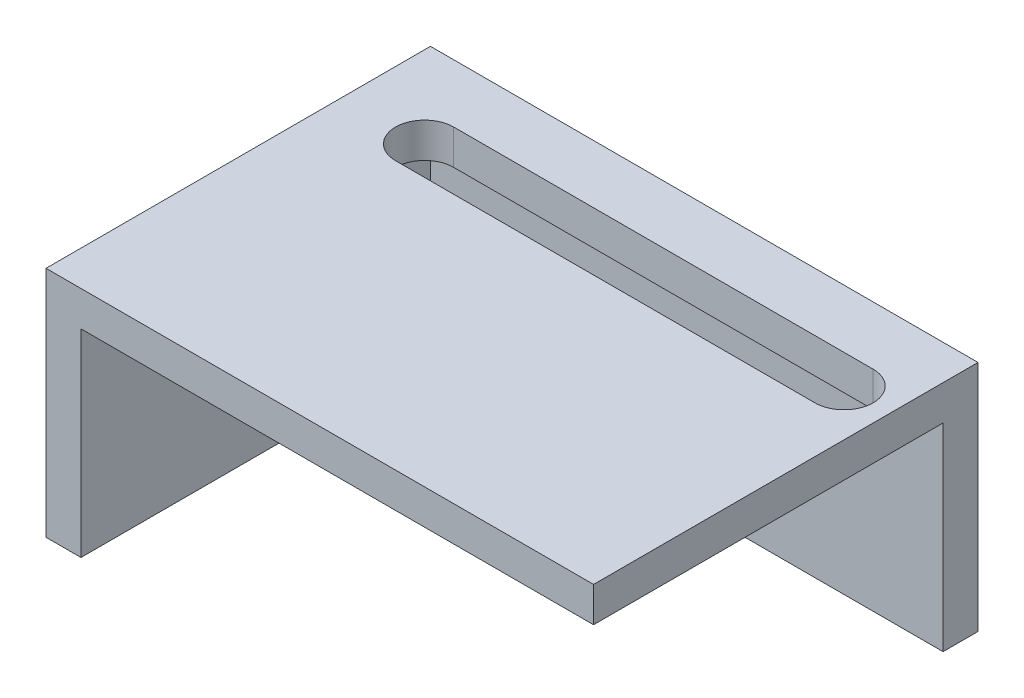
SolidWorks part; units mm, degrees
ref_plane "Front Plane" through (0, 0, 0) normal (0, 0, 1) x (1, 0, 0)
ref_plane "Top Plane" through (0, 0, 0) normal (0, 1, 0) x (1, 0, 0)
ref_plane "Right Plane" through (0, 0, 0) normal (1, 0, 0) x (0, 0, -1)
sketch "Sketch2" plane through (0, 0, 0) normal (0, 1, 0) x (1, 0, 0)
  line L1 (22, 15) -> (-22, 15)
  line L2 (22, 15) -> (22, -15)
  line L3 (22, -15) -> (-22, -15)
  line L4 (-22, 15) -> (-22, -15)
  line L5 (22, 15) -> (-22, -15) construction
  line L6 (22, -15) -> (-22, 15) construction
  point P0 (0, 0)
  dimension "D1" = 44
  dimension "D2" = 30
extrude "Boss-Extrude1" add sketch "Sketch2" along normal blind 3
sketch "Sketch3" plane through (0, 0, -15) normal (0, 0, -1) x (-1, 0, 0)
  line L1 (-22, 3) -> (22, 3)
  line L2 (-22, 3) -> (-22, -17)
  line L3 (-22, -17) -> (22, -17)
  line L4 (22, 3) -> (22, -17)
  dimension "D1" = 44
  dimension "D2" = 20
extrude "Boss-Extrude2" add sketch "Sketch3" along normal blind 3
sketch "Sketch4" plane through (-22, 0, 0) normal (-1, 0, 0) x (0, 0, 1)
  line L1 (-18, 3) -> (15, 3)
  line L2 (-18, 3) -> (-18, -17)
  line L3 (-18, -17) -> (15, -17)
  line L4 (15, 3) -> (15, -17)
  dimension "D1" = 33
  dimension "D2" = 20
extrude "Boss-Extrude3" add sketch "Sketch4" along normal blind 3
sketch "Sketch5" plane through (0, 0, 0) normal (0, -1, 0) x (1, 0, 0)
  line L0 (-18, -10.5) -> (18, -10.5) construction
  line L1 (-18, -8) -> (18, -8)
  line L2 (-18, -13) -> (18, -13)
  line L3 (22, -15) -> (-22, -15) construction
  line L4 (-22, -15) -> (-22, 15) construction
  line L5 (22, 15) -> (22, -15) construction
  arc A0 (-18, -8) -> (-18, -13) centre (-18, -10.5) ccw
  arc A1 (18, -13) -> (18, -8) centre (18, -10.5) ccw
  point P2 (0, -10.5)
  dimension "D2" = 4
  dimension "D3" = 4
  dimension "D1" = 2
  dimension "D4" = 5
extrude "Cut-Extrude1" cut sketch "Sketch5" against normal blind 3
